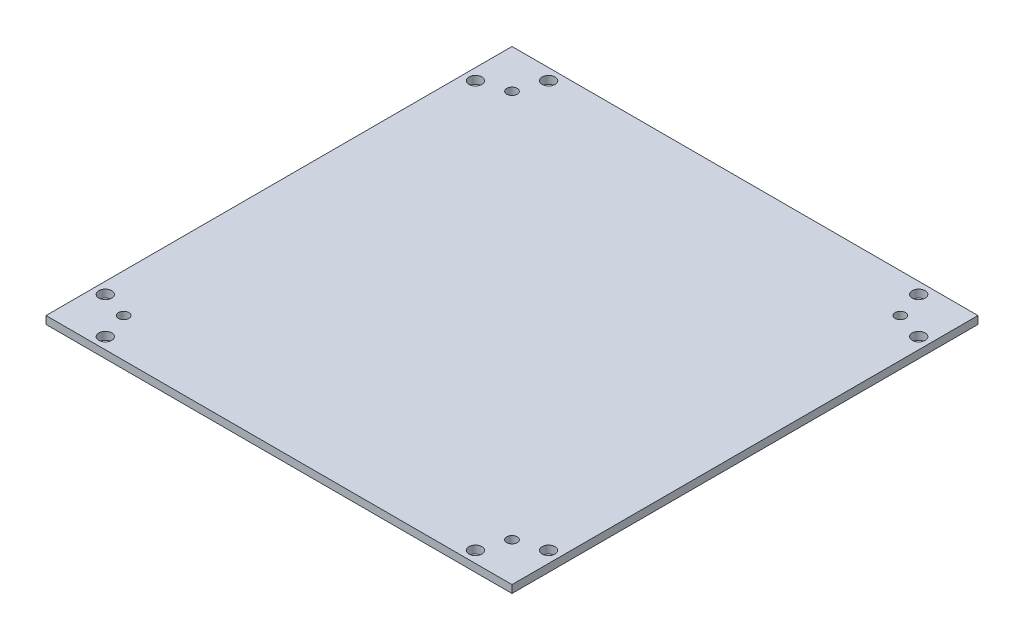
SolidWorks part; units mm, degrees
ref_plane "Front Plane" through (0, 0, 0) normal (0, 0, 1) x (1, 0, 0)
ref_plane "Top Plane" through (0, 0, 0) normal (0, 1, 0) x (1, 0, 0)
ref_plane "Right Plane" through (0, 0, 0) normal (1, 0, 0) x (0, 0, -1)
sketch "Sketch1" plane through (0, 0, 0) normal (0, 1, 0) x (1, 0, 0)
  line L0 (-71.4779, 85.6221) -> (-85.62, 71.48) construction
  line L1 (90, -90) -> (-90, -90)
  line L2 (90, -90) -> (90, 90)
  line L3 (90, 90) -> (-90, 90)
  line L4 (-90, -90) -> (-90, 90)
  line L5 (90, -90) -> (-90, 90) construction
  line L6 (90, 90) -> (-90, -90) construction
  circle A0 centre (-75, 75) radius 2
  circle A1 centre (75, 75) radius 2
  circle A2 centre (-75, -75) radius 2
  circle A3 centre (75, -75) radius 2
  circle A4 centre (-85.62, 71.48) radius 2.5
  circle A5 centre (-71.4779, 85.6221) radius 2.5
  circle A6 centre (85.6221, 71.4779) radius 2.5
  circle A7 centre (71.48, 85.62) radius 2.5
  circle A8 centre (71.4779, -85.6221) radius 2.5
  circle A9 centre (85.62, -71.48) radius 2.5
  circle A10 centre (-85.6221, -71.4779) radius 2.5
  circle A11 centre (-71.48, -85.62) radius 2.5
  point P0 (0, 0)
  point P33 (0, 0)
  dimension "D3" = 4
  dimension "D4" = 4
  dimension "D5" = 4
  dimension "D6" = 4
  dimension "D11" = 5
  dimension "D12" = 5
  dimension "D16" = 18.52
  dimension "D1" = 180
  dimension "D2" = 180
  dimension "D7" = 15
  dimension "D8" = 15
  dimension "D9" = 15
  dimension "D10" = 15
  dimension "D13" = 4.38
  dimension "D14" = 20
  dimension "D17" = 4
extrude "Boss-Extrude1" add sketch "Sketch1" along normal blind 3
